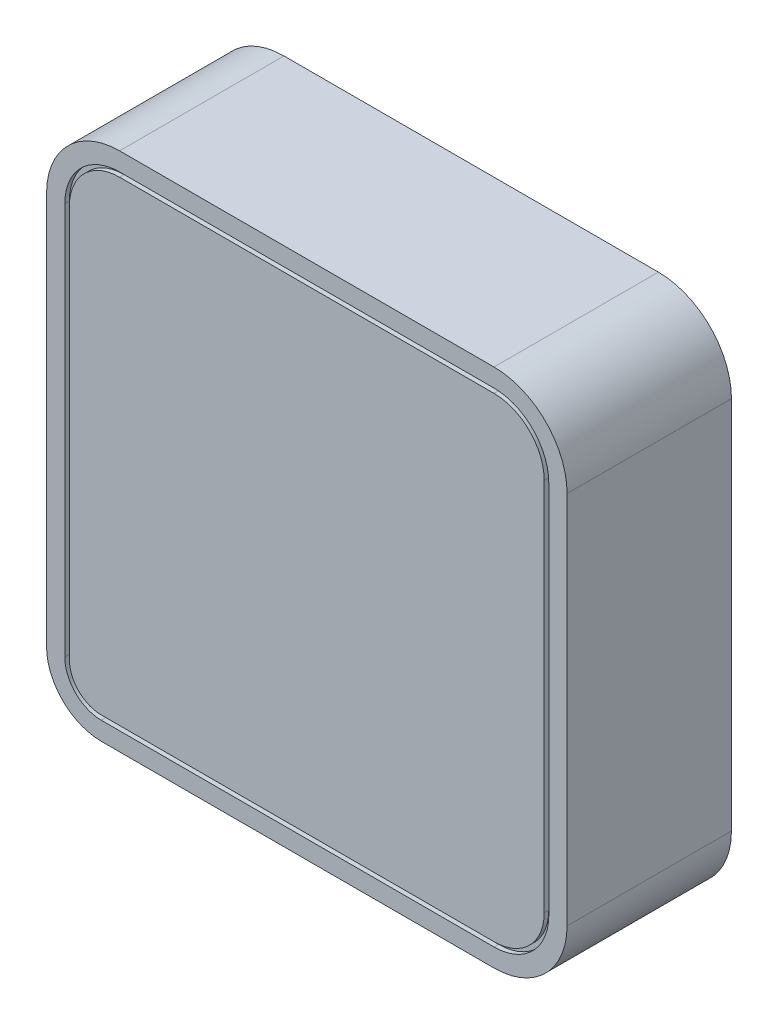
SolidWorks part; units mm, degrees
ref_plane "Alzado" through (0, 0, 0) normal (0, 0, 1) x (1, 0, 0)
ref_plane "Planta" through (0, 0, 0) normal (0, 1, 0) x (1, 0, 0)
ref_plane "Vista lateral" through (0, 0, 0) normal (1, 0, 0) x (0, 0, -1)
sketch "Croquis1" plane through (0, 0, 0) normal (0, 0, 1) x (1, 0, 0)
  line L1 (20.5, -28.5) -> (-22.5, -28.5)
  line L2 (28.5, -20.5) -> (28.5, 20.5)
  line L3 (20.5, 28.5) -> (-20.5, 28.5)
  line L4 (-28.5, -22.5) -> (-28.5, 20.5)
  line L5 (28.5, -28.5) -> (-28.5, 28.5) construction
  line L6 (28.5, 28.5) -> (-28.5, -28.5) construction
  arc A0 (28.5, 20.5) -> (20.5, 28.5) centre (20.5, 20.5) ccw
  arc A1 (20.5, -28.5) -> (28.5, -20.5) centre (20.5, -20.5) ccw
  arc A2 (-20.5, 28.5) -> (-28.5, 20.5) centre (-20.5, 20.5) ccw
  arc A3 (-22.5, -28.5) -> (-28.5, -22.5) centre (-22.5, -22.5) cw
  point P0 (0, 0)
  point P15 (-26.1569, 26.1569)
  point P16 (26.1569, -26.1569)
  dimension "D2" = 8
  dimension "D4" = 6
  dimension "D1" = 57
  dimension "D3" = 57
extrude "Saliente-Extruir1" add sketch "Croquis1" along normal blind 18
sketch "Croquis2" plane through (0, 0, 18) normal (0, 0, 1) x (1, 0, 0)
  line L4 (20.5, 28.5) -> (-20.5, 28.5)
  line L5 (-28.5, 20.5) -> (-28.5, -22.5)
  line L6 (-22.5, -28.5) -> (20.5, -28.5)
  line L7 (28.5, -20.5) -> (28.5, 20.5)
  line L8 (20.5, 28.5) -> (-20.5, 28.5) construction
  line L9 (-28.5, 20.5) -> (-28.5, -22.5) construction
  line L10 (-22.5, -28.5) -> (20.5, -28.5) construction
  line L11 (28.5, -20.5) -> (28.5, 20.5) construction
  line L12 (-26, 20.5) -> (-26, -22.5)
  line L13 (-22.5, -26) -> (20.5, -26)
  line L14 (26, -20.5) -> (26, 20.5)
  line L15 (20.5, 26) -> (-20.5, 26)
  line L16 (20.5, 26.5) -> (-20.5, 26.5)
  line L17 (-26.5, 20.5) -> (-26.5, -22.5)
  line L18 (-22.5, -26.5) -> (20.5, -26.5)
  line L19 (26.5, -20.5) -> (26.5, 20.5)
  line L20 (20.5, 26.5) -> (-20.5, 26.5)
  line L21 (-26.5, 20.5) -> (-26.5, -22.5)
  line L22 (-22.5, -26.5) -> (20.5, -26.5)
  line L23 (26.5, -20.5) -> (26.5, 20.5)
  arc A4 (28.5, 20.5) -> (20.5, 28.5) centre (20.5, 20.5) ccw
  arc A5 (-20.5, 28.5) -> (-28.5, 20.5) centre (-20.5, 20.5) ccw
  arc A6 (-28.5, -22.5) -> (-22.5, -28.5) centre (-22.5, -22.5) ccw
  arc A7 (20.5, -28.5) -> (28.5, -20.5) centre (20.5, -20.5) ccw
  arc A8 (28.5, 20.5) -> (20.5, 28.5) centre (20.5, 20.5) ccw construction
  arc A9 (-20.5, 28.5) -> (-28.5, 20.5) centre (-20.5, 20.5) ccw construction
  arc A10 (-28.5, -22.5) -> (-22.5, -28.5) centre (-22.5, -22.5) ccw construction
  arc A11 (20.5, -28.5) -> (28.5, -20.5) centre (20.5, -20.5) ccw construction
  arc A12 (-20.5, 26) -> (-26, 20.5) centre (-20.5, 20.5) ccw
  arc A13 (-26, -22.5) -> (-22.5, -26) centre (-22.5, -22.5) ccw
  arc A14 (20.5, -26) -> (26, -20.5) centre (20.5, -20.5) ccw
  arc A15 (26, 20.5) -> (20.5, 26) centre (20.5, 20.5) ccw
  arc A16 (26.5, 20.5) -> (20.5, 26.5) centre (20.5, 20.5) ccw
  arc A17 (-20.5, 26.5) -> (-26.5, 20.5) centre (-20.5, 20.5) ccw
  arc A18 (-26.5, -22.5) -> (-22.5, -26.5) centre (-22.5, -22.5) ccw
  arc A19 (20.5, -26.5) -> (26.5, -20.5) centre (20.5, -20.5) ccw
  arc A20 (26.5, 20.5) -> (20.5, 26.5) centre (20.5, 20.5) ccw
  arc A21 (-20.5, 26.5) -> (-26.5, 20.5) centre (-20.5, 20.5) ccw
  arc A22 (-26.5, -22.5) -> (-22.5, -26.5) centre (-22.5, -22.5) ccw
  arc A23 (20.5, -26.5) -> (26.5, -20.5) centre (20.5, -20.5) ccw
  dimension "D1" = 0
  dimension "D2" = 2
  dimension "D3" = 0.5
extrude "Cortar-Extruir1" cut sketch "Croquis2" against normal blind 0.5
sketch "Croquis3" plane through (-28.5, 0, 0) normal (-1, 0, 0) x (0, 0, 1)
  line L0 (18, 20.5) -> (18, -22.5) construction
  line L1 (15, 16.5) -> (3, 16.5)
  line L2 (15, 16.5) -> (15, 1.5)
  line L3 (15, 1.5) -> (3, 1.5)
  line L4 (3, 16.5) -> (3, 1.5)
  line L5 (0, 20.5) -> (0, -22.5) construction
  line L6 (18, 28.5) -> (0, 28.5) construction
  line L7 (9, -3.5) -> (7.3, -3.5)
  line L8 (7.3, -3.5) -> (5.7, -5.1)
  line L9 (5.7, -5.1) -> (5.7, -10.3)
  line L10 (5.7, -10.3) -> (7.3, -11.9)
  line L11 (7.3, -11.9) -> (9, -11.9)
  line L12 (9, -11.9) -> (9, -3.5)
  line L13 (7.3, -3.5) -> (7.3, -11.9) construction
  line L14 (9, -11.9) -> (9, -18.4) construction
  line L15 (9, -18.4) -> (7.75, -18.4) construction
  circle A0 centre (7.75, -18.4) radius 1.25
  dimension "D10" = 2.5
  dimension "D1" = 3
  dimension "D2" = 3
  dimension "D3" = 12
  dimension "D4" = 15
  dimension "D5" = 3.3
  dimension "D6" = 1.7
  dimension "D7" = 8.4
  dimension "D8" = 9
  dimension "D9" = 5
  dimension "D11" = 6.5
extrude "Cortar-Extruir2" cut sketch "Croquis3" against normal blind 0.5
